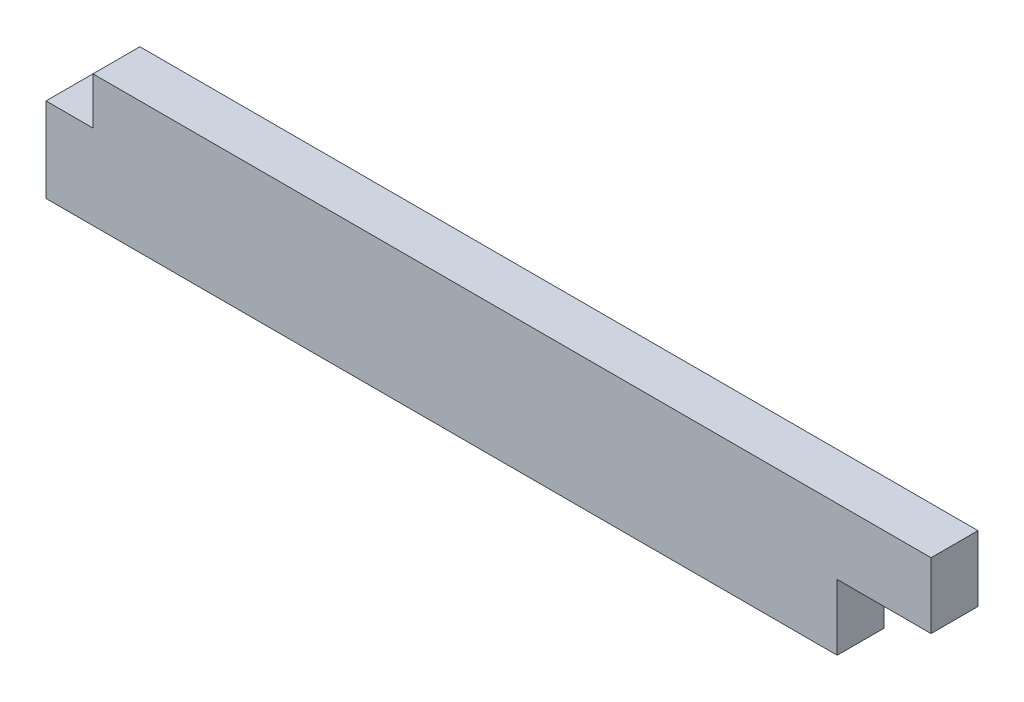
SolidWorks part; units mm, degrees
material "Фанера"
ref_plane "Front Plane" through (0, 0, 0) normal (0, 0, 1) x (1, 0, 0)
ref_plane "Top Plane" through (0, 0, 0) normal (0, 1, 0) x (1, 0, 0)
ref_plane "Right Plane" through (0, 0, 0) normal (1, 0, 0) x (0, 0, -1)
sketch "Эскиз1" plane through (0, 0, 0) normal (0, 0, 1) x (1, 0, 0)
  line L1 (-31.1429, -2.8) -> (13.2571, -2.8)
  line L2 (-33.9429, 0) -> (-33.9429, 2.24)
  line L3 (-31.1429, 5.04) -> (18.8571, 5.04)
  line L4 (18.8571, 1.12) -> (18.8571, 5.04)
  line L5 (-32.7116, -8.7429) -> (18.8571, 5.04) construction
  line L6 (-33.9429, 5.04) -> (18.8571, -2.8) construction
  line L8 (18.8571, 1.12) -> (13.2571, 1.12)
  line L9 (13.2571, 1.12) -> (13.2571, -2.8)
  line L10 (-33.9429, 0) -> (-33.9429, -2.8)
  line L11 (-33.9429, -2.8) -> (-31.1429, -2.8)
  line L12 (-33.9429, 2.24) -> (-31.1429, 2.24)
  line L13 (-31.1429, 2.24) -> (-31.1429, 5.04)
  point P0 (0, 0)
  dimension "D1" = 52.8
  dimension "D2" = 7.84
  dimension "D5" = 5.6
  dimension "D3" = 2.8
  dimension "D4" = 5.04
extrude "Бобышка-Вытянуть1" add sketch "Эскиз1" along normal mid plane 2.8
equation "\"thickness\"= 2.8"
equation "\"D1@Эскиз1\"=\"thickness\"+50"
equation "\"D2@Эскиз1\"=\"thickness\"+\"thickness\"*1.8"
equation "\"D5@Эскиз1\"=\"thickness\"*2"
equation "\"D1@Бобышка-Вытянуть1\"=\"thickness\""
equation "\"D3@Эскиз1\"=\"thickness\""
equation "\"D4@Эскиз1\"=\"thickness\"*1.8"
